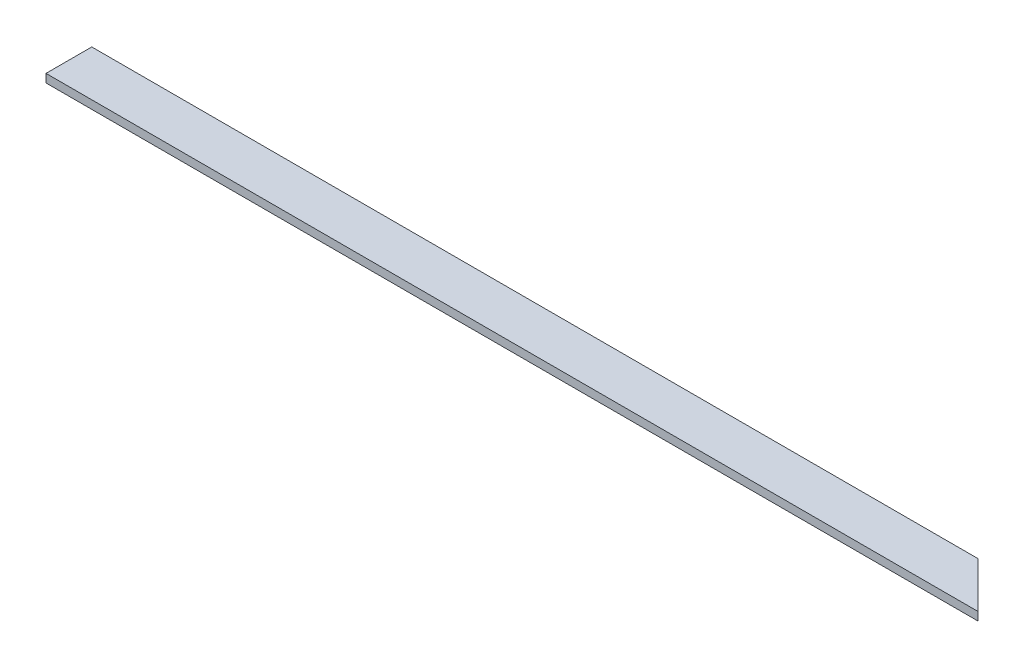
SolidWorks part; units mm, degrees
ref_plane "Front Plane" through (0, 0, 0) normal (0, 0, 1) x (1, 0, 0)
ref_plane "Top Plane" through (0, 0, 0) normal (0, 1, 0) x (1, 0, 0)
ref_plane "Right Plane" through (0, 0, 0) normal (1, 0, 0) x (0, 0, -1)
sketch "Sketch1" plane through (0, 0, 0) normal (0, 1, 0) x (1, 0, 0)
  line L0 (0, 0) -> (0, 139.7)
  line L1 (0, 0) -> (2844.8, 0)
  line L2 (2844.8, 0) -> (2705.1, 139.7)
  line L3 (0, 139.7) -> (2705.1, 139.7)
  line L5 (2844.8, 0) -> (2705.1, 0)
  dimension "D1" = 2844.8
  dimension "D2" = 139.7
extrude "Boss-Extrude1" add sketch "Sketch1" along normal blind 25.4
